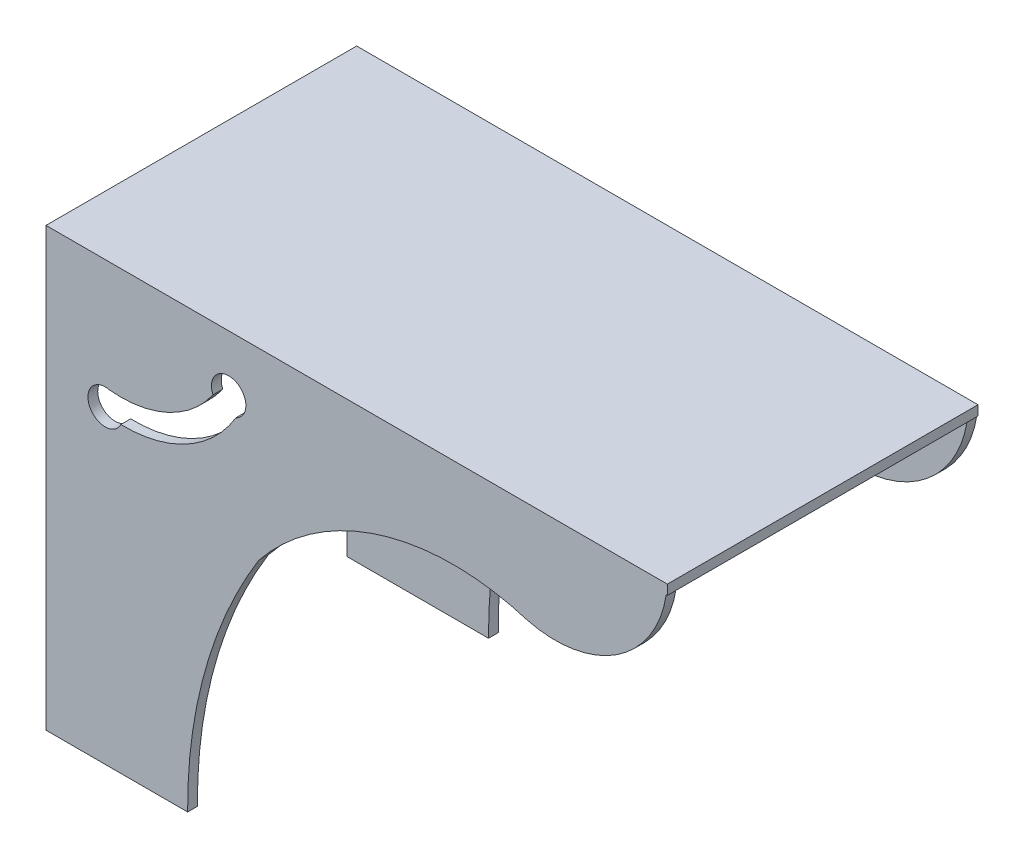
SolidWorks part; units mm, degrees
material "1060 Alloy"
ref_plane "Front Plane" through (0, 0, 0) normal (0, 0, 1) x (1, 0, 0)
ref_plane "Top Plane" through (0, 0, 0) normal (0, 1, 0) x (1, 0, 0)
ref_plane "Right Plane" through (0, 0, 0) normal (1, 0, 0) x (0, 0, -1)
sketch "Sketch1" plane through (0, 0, 0) normal (0, 1, 0) x (1, 0, 0)
  line L1 (-31.75, 15.875) -> (31.75, 15.875)
  line L2 (-31.75, 15.875) -> (-31.75, -15.875)
  line L3 (-31.75, -15.875) -> (31.75, -15.875)
  line L4 (31.75, 15.875) -> (31.75, -15.875)
  line L5 (0, -15.875) -> (0, 15.875) construction
  line L6 (-31.75, 0) -> (31.75, 0) construction
  point P0 (0, 0)
  dimension "D1" = 63.5
  dimension "D2" = 31.75
extrude "Boss-Extrude1" add sketch "Sketch1" along normal blind 1
ref_plane "Plane1" through (0, 0, -15.875) normal (0, 0, -1) x (-1, 0, 0)
sketch "Sketch2" plane through (0, 0, -15.875) normal (0, 0, -1) x (-1, 0, 0)
  line L0 (31.75, -17.7892) -> (31.75, -43.6825)
  line L1 (-31.75, 1) -> (31.75, 1)
  line L4 (31.75, 1) -> (31.75, -17.7892)
  line L5 (17.2744, -43.6825) -> (31.75, -43.6825)
  arc A0 (-31.75, 1) -> (-17.4534, -9.3504) centre (-20.2916, 1.7782) ccw
  arc A1 (-17.4534, -9.3504) -> (10.0201, -17.7892) centre (-9.8977, -33.693) cw
  arc A2 (10.0201, -17.7892) -> (17.2744, -43.6825) centre (-31.1951, -43.2989) cw
  arc A3 (14.6822, -5.4618) -> (25.2846, -10.3205) centre (24.0969, 1.0852) ccw
  arc A4 (12.3536, -6.3352) -> (24.0969, -12.7977) centre (23.7461, 0.4657) ccw
  arc A6 (14.6822, -5.4618) -> (12.3536, -6.3352) centre (13.0813, -4.7342) ccw
  arc A7 (25.2846, -10.3205) -> (24.0969, -12.7977) centre (25.6949, -12.0406) cw
extrude "Boss-Extrude2" add sketch "Sketch2" against normal blind 1
mirror "Mirror1" about plane through (0, 0, 0) normal (0, 0, 1) of "Boss-Extrude2"
